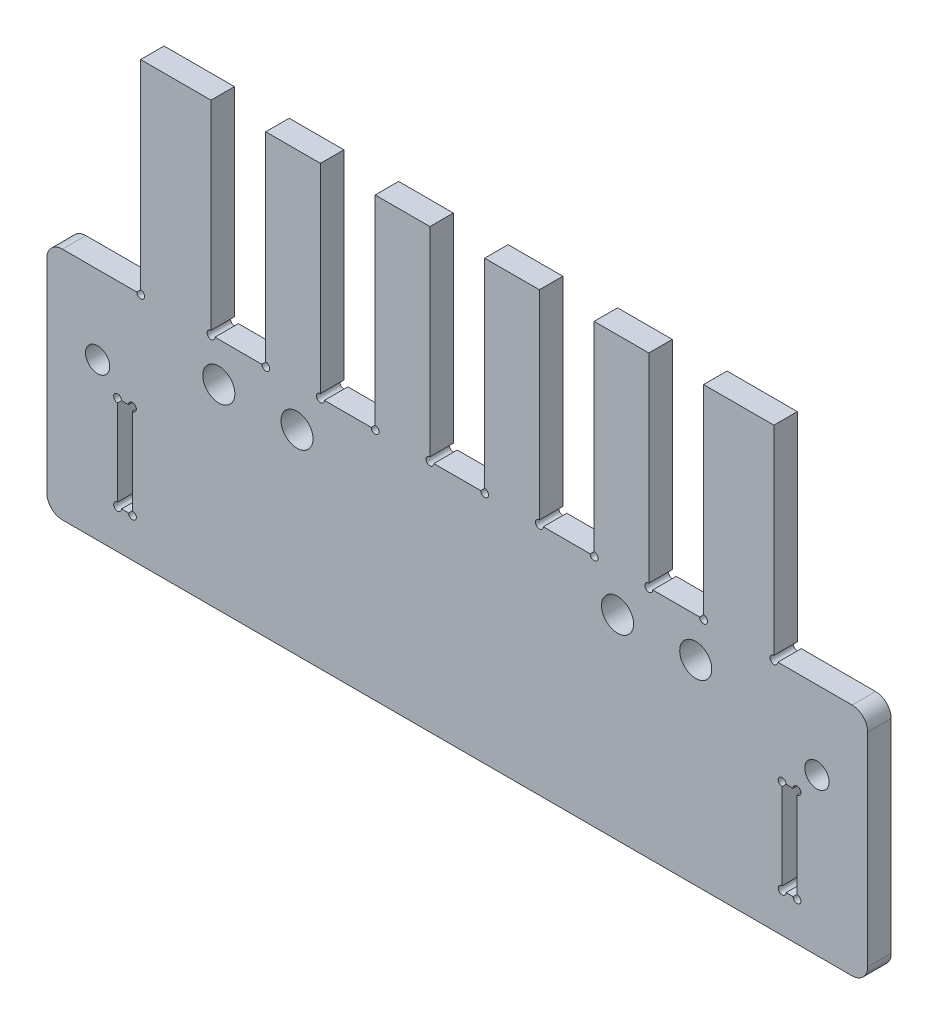
SolidWorks part; units mm, degrees
material "Thornel Mat VMA"
ref_plane "前视基准面" through (0, 0, 0) normal (0, 0, 1) x (1, 0, 0)
ref_plane "上视基准面" through (0, 0, 0) normal (0, 1, 0) x (1, 0, 0)
ref_plane "右视基准面" through (0, 0, 0) normal (1, 0, 0) x (0, 0, -1)
sketch "草图1" plane through (0, 0, 0) normal (0, 0, 1) x (1, 0, 0)
  line L1 (-52.5, -26.75) -> (52.5, -26.75)
  line L2 (-52.5, -26.75) -> (-52.5, 26.75)
  line L3 (-52.5, 26.75) -> (52.5, 26.75)
  line L4 (52.5, -26.75) -> (52.5, 26.75)
  line L5 (-52.5, -26.75) -> (52.5, 26.75) construction
  line L6 (-52.5, 26.75) -> (52.5, -26.75) construction
  point P0 (0, 0)
  dimension "D1" = 53.5
  dimension "D2" = 105
extrude "凸台-拉伸1" add sketch "草图1" along normal blind 3
sketch "草图2" plane through (0, 0, 0) normal (0, 0, -1) x (-1, 0, 0)
  line L0 (-52.5, -26.75) -> (-52.5, 26.75) construction
  line L1 (41.5, -24.25) -> (43.5, -24.25)
  line L2 (41.5, -24.25) -> (41.5, -12.25)
  line L3 (41.5, -12.25) -> (43.5, -12.25)
  line L4 (43.5, -24.25) -> (43.5, -12.25)
  line L5 (-43.5, -24.25) -> (-41.5, -24.25)
  line L6 (-43.5, -24.25) -> (-43.5, -12.25)
  line L7 (-43.5, -12.25) -> (-41.5, -12.25)
  line L8 (-41.5, -24.25) -> (-41.5, -12.25)
  line L9 (52.5, 26.75) -> (52.5, -26.75) construction
  line L10 (52.5, -26.75) -> (-52.5, -26.75) construction
  circle A0 centre (46, -9.25) radius 1.55
  circle A1 centre (-46, -9.25) radius 1.55
  dimension "D13" = 3.1
  dimension "D14" = 3.1
  dimension "D1" = 9
  dimension "D2" = 9
  dimension "D3" = 2.5
  dimension "D4" = 2.5
  dimension "D5" = 12
  dimension "D6" = 12
  dimension "D7" = 2
  dimension "D8" = 2
  dimension "D9" = 6.5
  dimension "D10" = 17.5
  dimension "D11" = 6.5
  dimension "D12" = 17.5
extrude "切除-拉伸1" cut sketch "草图2" against normal blind 5
sketch "草图3" plane through (0, 0, 0) normal (0, 0, -1) x (-1, 0, 0)
  line L0 (52.5, 26.75) -> (52.5, -26.75) construction
  line L1 (52.5, 0.75) -> (40.5, 0.75)
  line L2 (52.5, 0.75) -> (52.5, 26.75)
  line L3 (52.5, 26.75) -> (40.5, 26.75)
  line L4 (40.5, 0.75) -> (40.5, 26.75)
  line L5 (-52.5, 26.75) -> (52.5, 26.75) construction
  line L6 (52.5, -26.75) -> (-52.5, -26.75) construction
  line L7 (-52.5, -26.75) -> (-52.5, 26.75) construction
  line L8 (-52.5, 0.75) -> (-40.5, 0.75)
  line L9 (-52.5, 0.75) -> (-52.5, 26.75)
  line L10 (-52.5, 26.75) -> (-40.5, 26.75)
  line L11 (-40.5, 0.75) -> (-40.5, 26.75)
  line L12 (-52.5, 0.75) -> (52.5, 0.75)
  line L13 (-31.5, 0.75) -> (-24.5, 0.75)
  line L14 (-31.5, 0.75) -> (-31.5, 26.75)
  line L15 (-31.5, 26.75) -> (-24.5, 26.75)
  line L16 (-24.5, 0.75) -> (-24.5, 26.75)
  line L17 (-17.5, 0.75) -> (-10.5, 0.75)
  line L18 (-17.5, 0.75) -> (-17.5, 26.75)
  line L19 (-17.5, 26.75) -> (-10.5, 26.75)
  line L20 (-10.5, 0.75) -> (-10.5, 26.75)
  line L21 (24.5, 0.75) -> (31.5, 0.75)
  line L22 (24.5, 0.75) -> (24.5, 26.75)
  line L23 (24.5, 26.75) -> (31.5, 26.75)
  line L24 (31.5, 0.75) -> (31.5, 26.75)
  line L25 (-3.5, 26.75) -> (3.5, 26.75)
  line L26 (-3.5, 26.75) -> (-3.5, 0.75)
  line L27 (-3.5, 0.75) -> (3.5, 0.75)
  line L28 (3.5, 26.75) -> (3.5, 0.75)
  line L31 (22, 0.75) -> (29, 0.75)
  line L33 (-52.5, 0.75) -> (52.5, 0.75)
  line L35 (10.5, 26.75) -> (17.5, 26.75)
  line L36 (10.5, 26.75) -> (10.5, 0.75)
  line L37 (10.5, 0.75) -> (17.5, 0.75)
  line L38 (17.5, 26.75) -> (17.5, 0.75)
  line M35 (52.5, -26.75) -> (52.5, 26.75)
  line M36 (52.5, 26.75) -> (-52.5, 26.75)
  dimension "D1" = 27.5
  dimension "D2" = 12
  dimension "D3" = 12
  dimension "D4" = 27.5
  dimension "D5" = 7
  dimension "D6" = 7
  dimension "D7" = 7
  dimension "D8" = 9
  dimension "D9" = 9
  dimension "D10" = 7
  dimension "D11" = 7
  dimension "D12" = 7
  dimension "D13" = 7
  dimension "D14" = 7
  dimension "D15" = 7
extrude "切除-拉伸2" cut sketch "草图3" against normal through all contours L12 L16 L14 M36 | L12 L20 L18 M36 | L4 L1 M35 M36 | L22 L21 L24 L23 | L26 L25 L28 L27 | L9 L8 L11 L10 | L36 L35 L38 L37
sketch "草图4" plane through (0, 0, 0) normal (0, 0, -1) x (-1, 0, 0)
  line L0 (-17.5, 0.75) -> (-10.5, 0.75) construction
  circle A0 centre (0, -14.25) radius 2.5
  dimension "D1" = 5
  dimension "D2" = 15
extrude "切除-拉伸3" [suppressed] cut sketch "草图4" against normal through all
sketch "草图5" plane through (0, 0, 0) normal (0, 0, -1) x (-1, 0, 0)
  line L0 (41.5, -12.25) -> (41.5, -24.25) construction
  line L1 (24.5, 0.75) -> (31.5, 0.75) construction
  line L2 (-31.5, 0.75) -> (-24.5, 0.75) construction
  line L3 (-41.5, -24.25) -> (-41.5, -12.25) construction
  circle A0 centre (33.5, -14.25) radius 2.5
  circle A1 centre (-33.5, -14.25) radius 2.5
  dimension "D1" = 5
  dimension "D4" = 5
  dimension "D2" = 8
  dimension "D3" = 15
  dimension "D5" = 15
  dimension "D6" = 8
extrude "切除-拉伸4" [suppressed] cut sketch "草图5" against normal blind 10
sketch "草图6" plane through (0, 0, 0) normal (0, 0, -1) x (-1, 0, 0)
  line L0 (0, 7.589) -> (0, -30.5527) construction
  line L1 (-31.5, 0.75) -> (-24.5, 0.75) construction
  circle A0 centre (-15, -9.25) radius 2.5
  circle A1 centre (15, -9.25) radius 2.5
  dimension "D1" = 5
  dimension "D2" = 5
  dimension "D3" = 15
  dimension "D4" = 15
  dimension "D5" = 10
sketch "草图7" plane through (0, 0, 0) normal (0, 0, -1) x (-1, 0, 0)
  line L0 (-3.5, 0.75) -> (3.5, 0.75) construction
  line L1 (3.5, 26.75) -> (3.5, 0.75) construction
  circle A0 centre (-40.5, 0.75) radius 0.5
  circle A1 centre (-31.5, 0.75) radius 0.5
  circle A2 centre (-24.5, 0.75) radius 0.5
  circle A3 centre (-17.5, 0.75) radius 0.5
  circle A4 centre (-10.5, 0.75) radius 0.5
  circle A5 centre (24.5, 0.75) radius 0.5
  circle A6 centre (31.5, 0.75) radius 0.5
  circle A7 centre (40.5, 0.75) radius 0.5
  circle A8 centre (-3.5, 0.75) radius 0.5
  circle A9 centre (3.5, 0.75) radius 0.5
  circle A12 centre (10.5, 0.75) radius 0.5
  circle A13 centre (17.5, 0.75) radius 0.5
  dimension "D1" = 1
  dimension "D2" = 1
  dimension "D3" = 1
  dimension "D4" = 1
  dimension "D5" = 1
sketch "草图8" plane through (0, 0, 0) normal (0, 0, -1) x (-1, 0, 0)
  line L0 (52.5, -26.75) -> (52.5, -29.25)
  line L1 (52.5, -26.75) -> (-52.5, -26.75) construction
  line L2 (52.5, -29.25) -> (-52.5, -29.25)
  line L3 (-52.5, -29.25) -> (-52.5, -26.75)
  line L4 (-52.5, -26.75) -> (52.5, -26.75)
  line L5 (-52.5, -26.75) -> (-52.5, 0.75) construction
  line L6 (52.5, 0.75) -> (52.5, -26.75) construction
  dimension "D1" = 2.5
extrude "凸台-拉伸2" add sketch "草图8" against normal blind 3
fillet "圆角1" radius 2 4 edges at (-52.5, 0.75, 1.5) (52.5, 0.75, 1.5) (52.5, -29.25, 1.5) (-52.5, -29.25, 1.5)
extrude "切除-拉伸6" cut sketch "草图7" against normal blind 10
sketch "草图10" plane through (0, 0, 0) normal (0, 0, -1) x (-1, 0, 0)
  line L0 (43.5, -12.25) -> (41.5, -12.25) construction
  line L1 (43.5, -24.25) -> (43.45, -24.25)
  line L2 (43.5, -24.25) -> (43.5, -12.25)
  line L3 (43.5, -12.25) -> (43.45, -12.25)
  line L4 (43.45, -24.25) -> (43.45, -12.25)
  line L5 (41.5, -24.25) -> (43.5, -24.25) construction
  line L6 (41.5, -24.25) -> (41.55, -24.25)
  line L7 (41.5, -24.25) -> (41.5, -12.25)
  line L8 (41.5, -12.25) -> (41.55, -12.25)
  line L9 (41.55, -24.25) -> (41.55, -12.25)
  line L10 (41.5, -12.25) -> (41.5, -24.25) construction
  line L11 (-41.5, -12.25) -> (-43.5, -12.25) construction
  line L12 (-41.5, -24.25) -> (-41.55, -24.25)
  line L13 (-41.5, -24.25) -> (-41.5, -12.25)
  line L14 (-41.5, -12.25) -> (-41.55, -12.25)
  line L15 (-41.55, -24.25) -> (-41.55, -12.25)
  line L17 (-43.5, -24.25) -> (-43.45, -24.25)
  line L18 (-43.5, -24.25) -> (-43.5, -12.25)
  line L19 (-43.5, -12.25) -> (-43.45, -12.25)
  line L20 (-43.45, -24.25) -> (-43.45, -12.25)
  dimension "D1" = 0.05
  dimension "D2" = 0.05
  dimension "D3" = 0.05
  dimension "D4" = 0.05
extrude "凸台-拉伸3" add sketch "草图10" against normal up to surface (3 mm away) up to face at (-42.5, -18.25, 3)
sketch "草图11" plane through (0, 0, 0) normal (0, 0, -1) x (-1, 0, 0)
  circle A0 centre (43.45, -24.25) radius 0.5
  circle A1 centre (41.55, -24.25) radius 0.5
  circle A2 centre (43.45, -12.25) radius 0.5
  circle A3 centre (41.55, -12.25) radius 0.5
  circle A4 centre (-41.55, -24.25) radius 0.5
  circle A5 centre (-43.45, -24.25) radius 0.5
  circle A6 centre (-43.45, -12.25) radius 0.5
  circle A7 centre (-41.55, -12.25) radius 0.5
  dimension "D1" = 1
extrude "切除-拉伸7" cut sketch "草图11" against normal blind 10
sketch "草图12" plane through (0, 0, 0) normal (0, 0, -1) x (-1, 0, 0)
  line L0 (0, 0) -> (0, -29.25) construction
  line L1 (0, 7.589) -> (0, -30.5527) construction
  line L2 (-50.5, -29.25) -> (50.5, -29.25) construction
  line L3 (-40.9315, -4.25) -> (41.2715, -4.25) construction
  line L4 (-50.5, 0.75) -> (-41, 0.75) construction
  line L5 (-52.5, -27.25) -> (-52.5, -1.25) construction
  circle A0 centre (-30.5, -4.25) radius 2.05
  circle A2 centre (-20.5, -4.25) radius 2.05
  circle A3 centre (20.5, -4.25) radius 2.05
  circle A4 centre (30.5, -4.25) radius 2.05
  dimension "D2" = 4.1
  dimension "D4" = 2
  dimension "D1" = 5
  dimension "D3" = 22
  dimension "D5" = 10
extrude "切除-拉伸8" cut sketch "草图12" against normal blind 10
